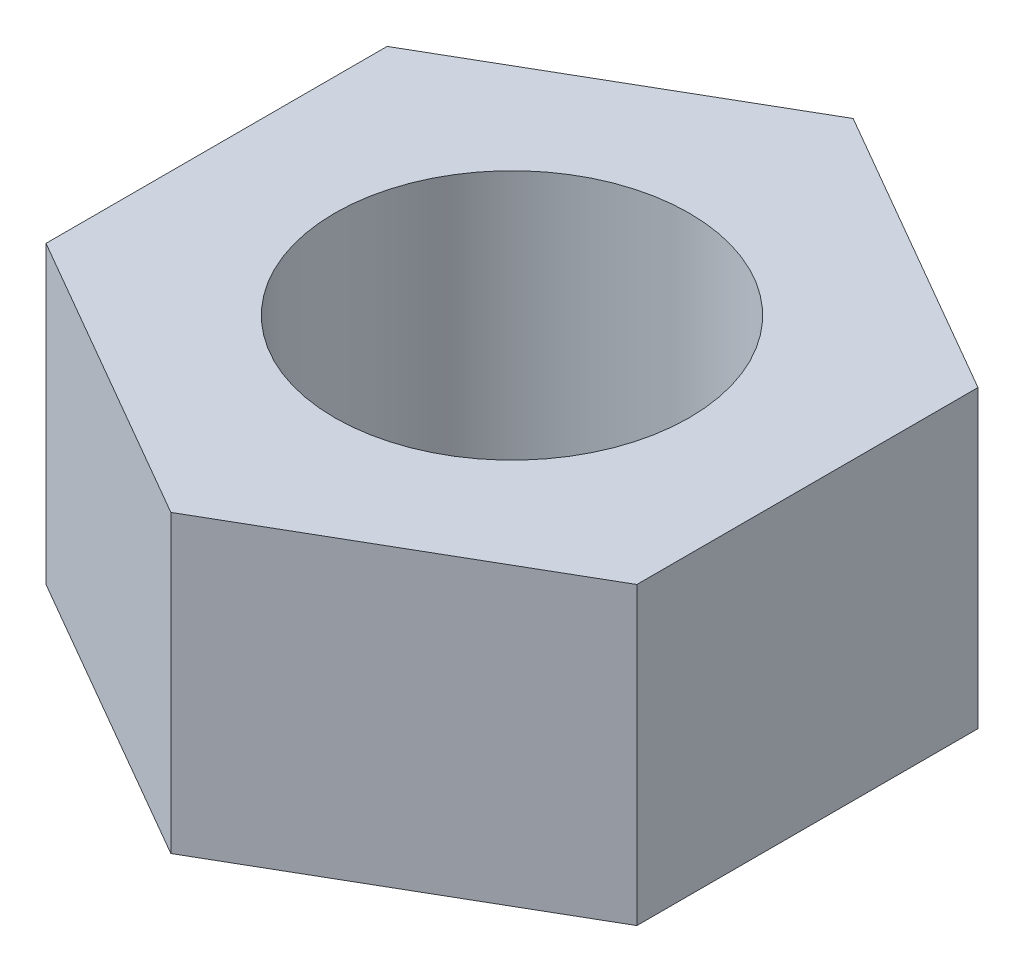
SolidWorks part; units mm, degrees
ref_plane "Front Plane" through (0, 0, 0) normal (0, 0, 1) x (1, 0, 0)
ref_plane "Top Plane" through (0, 0, 0) normal (0, 1, 0) x (1, 0, 0)
ref_plane "Right Plane" through (0, 0, 0) normal (1, 0, 0) x (0, 0, -1)
sketch "Sketch1" plane through (0, 0, 0) normal (0, 1, 0) x (1, 0, 0)
  line L1 (0, 2.8868) -> (-2.5, 1.4434)
  line L2 (-2.5, 1.4434) -> (-2.5, -1.4434)
  line L3 (-2.5, -1.4434) -> (0, -2.8868)
  line L4 (0, -2.8868) -> (2.5, -1.4434)
  line L5 (2.5, -1.4434) -> (2.5, 1.4434)
  line L6 (2.5, 1.4434) -> (0, 2.8868)
  circle A0 centre (0, 0) radius 2.5 construction
  circle A1 centre (0, 0) radius 1.5
  dimension "D2" = 3
  dimension "D1" = 5
extrude "Boss-Extrude1" add sketch "Sketch1" along normal blind 2.5
